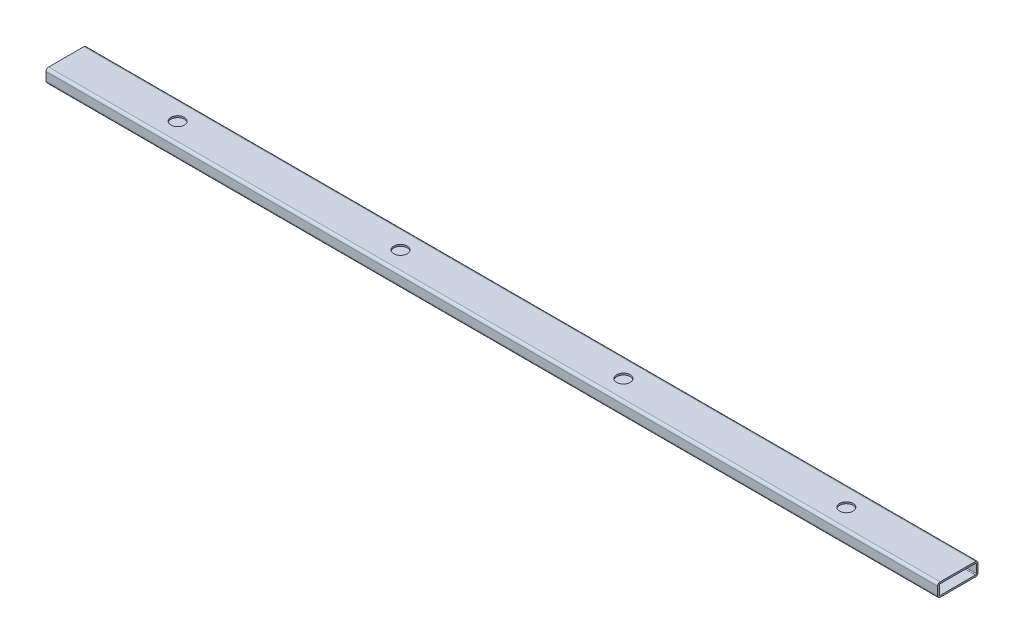
SolidWorks part; units mm, degrees
material "Plain Carbon Steel"
ref_plane "Front Plane" through (0, 0, 0) normal (0, 0, 1) x (1, 0, 0)
ref_plane "Top Plane" through (0, 0, 0) normal (0, 1, 0) x (1, 0, 0)
ref_plane "Right Plane" through (0, 0, 0) normal (1, 0, 0) x (0, 0, -1)
sketch "Sketch1" plane through (0, 0, 0) normal (1, 0, 0) x (0, 0, -1)
  line L0 (33.3248, 22.225) -> (-33.3248, 22.225)
  line L1 (33.3248, 25.4) -> (-33.3248, 25.4)
  line L2 (38.1, 20.6248) -> (38.1, 4.7752)
  line L3 (33.3248, 0) -> (-33.3248, 0)
  line L4 (-38.1, 20.6248) -> (-38.1, 4.7752)
  line L5 (-34.925, 20.6248) -> (-34.925, 4.7752)
  line L6 (33.3248, 3.175) -> (-33.3248, 3.175)
  line L7 (34.925, 20.6248) -> (34.925, 4.7752)
  arc A0 (38.1, 20.6248) -> (33.3248, 25.4) centre (33.3248, 20.6248) ccw
  arc A1 (38.1, 4.7752) -> (33.3248, 0) centre (33.3248, 4.7752) cw
  arc A2 (-33.3248, 0) -> (-38.1, 4.7752) centre (-33.3248, 4.7752) cw
  arc A3 (-38.1, 20.6248) -> (-33.3248, 25.4) centre (-33.3248, 20.6248) cw
  arc A4 (-34.925, 20.6248) -> (-33.3248, 22.225) centre (-33.3248, 20.6248) cw
  arc A5 (-33.3248, 3.175) -> (-34.925, 4.7752) centre (-33.3248, 4.7752) cw
  arc A6 (34.925, 4.7752) -> (33.3248, 3.175) centre (33.3248, 4.7752) cw
  arc A7 (34.925, 20.6248) -> (33.3248, 22.225) centre (33.3248, 20.6248) ccw
  point P5 (0, 0)
  dimension "D1" = 4.7752
  dimension "D2" = 25.4
  dimension "D3" = 76.2
  dimension "D4" = 3.175
extrude "Boss-Extrude1" add sketch "Sketch1" along normal mid plane 1682.75
sketch "Sketch2" plane through (0, 25.4, 0) normal (0, 1, 0) x (1, 0, 0)
  circle A0 centre (-631.0312, 0) radius 12.7
  dimension "D1" = 631.0312
  dimension "D2" = 25.4
extrude "Cut-Extrude1" cut sketch "Sketch2" against normal up to next (3.175 mm away)
pattern_linear "LPattern1" count 4 spacing 420.6875 along (1, 0, 0) of "Cut-Extrude1"
